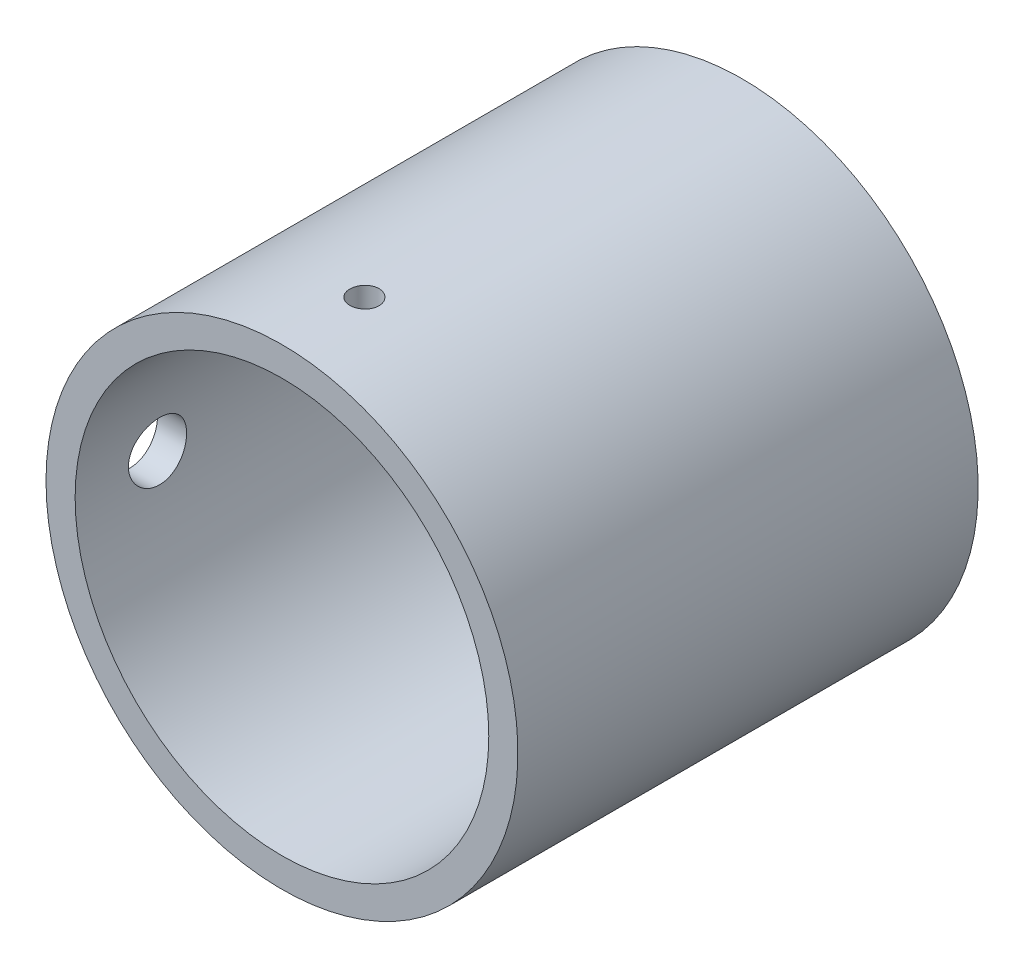
SolidWorks part; units mm, degrees
ref_plane "Front Plane" through (0, 0, 0) normal (0, 0, 1) x (1, 0, 0)
ref_plane "Top Plane" through (0, 0, 0) normal (0, 1, 0) x (1, 0, 0)
ref_plane "Right Plane" through (0, 0, 0) normal (1, 0, 0) x (0, 0, -1)
sketch "Sketch1" plane through (0, 0, 0) normal (0, 0, 1) x (1, 0, 0)
  circle A0 centre (0, 0) radius 7.1
  circle A1 centre (0, 0) radius 8.1
  dimension "D1" = 14.2
  dimension "D2" = 16.2
extrude "Boss-Extrude1" add sketch "Sketch1" along normal up to surface (1.3875 mm away) and the other way up to surface (14.4125 mm away)
sketch "Sketch3" plane through (0, 0, 0) normal (1, 0, 0) x (0, 0, -1)
  circle A0 centre (1.4407, 0) radius 1
  dimension "D1" = 2
sketch "Sketch4" plane through (0, 0, 0) normal (0, 1, 0) x (1, 0, 0)
  line L0 (0, 0.4407) -> (0, 2.4407) construction
  circle A0 centre (0, 1.4407) radius 0.5
  dimension "D1" = 1
extrude "Cut-Extrude1" cut sketch "Sketch3" against normal through all
extrude "Cut-Extrude2" cut sketch "Sketch4" along normal through all
